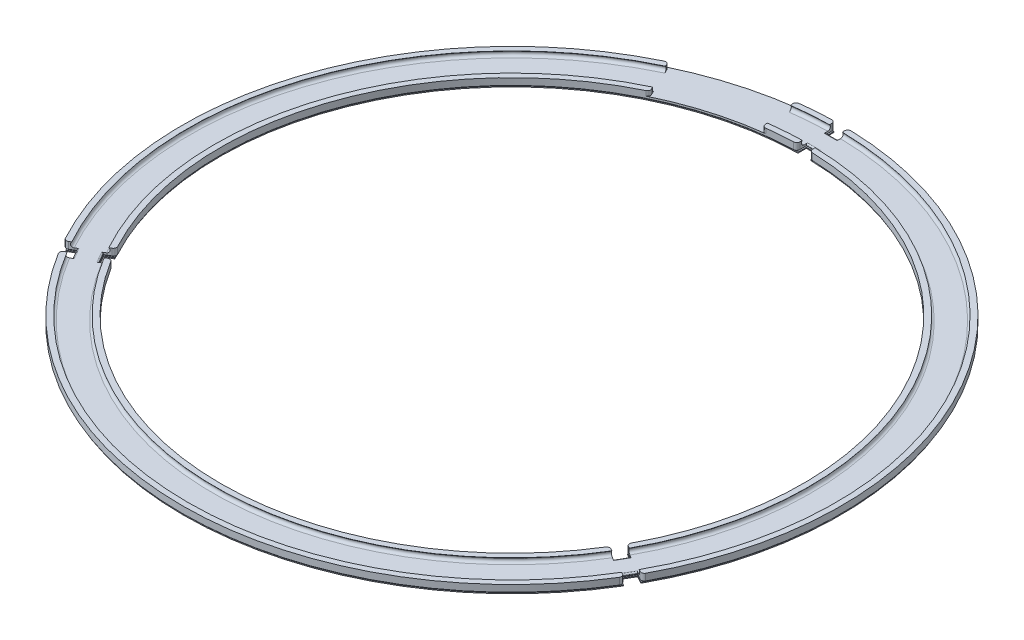
SolidWorks part; units mm, degrees
other "ferrite_sheet"
other "inductive_coil_frame" parameters "D1"=157.7465, "D2"=9.4909, "D3"=13.3244, "D4"=4.0567, "D5"=1.45, "D6"=1.6886
material "ABS"
ref_plane "Front Plane" through (0, 0, 0) normal (0, 0, 1) x (1, 0, 0)
ref_plane "Top Plane" through (0, 0, 0) normal (0, 1, 0) x (1, 0, 0)
ref_plane "Right Plane" through (0, 0, 0) normal (1, 0, 0) x (0, 0, -1)
sketch "Sketch1" plane through (0, 0, 0) normal (0, 0, 1) x (1, 0, 0)
  line L0 (0, 52.6316) -> (0, -56.2554) construction
  line L1 (93.5, 0) -> (100.9, 0) construction
  line L2 (91.2, 0.65) -> (92.9523, 0.65)
  line L3 (91.2, 0.65) -> (91.2, -1.85)
  line L4 (91.2, -1.85) -> (103.2, -1.85)
  line L5 (103.2, -1.85) -> (103.2, 0.65)
  line L6 (101.4477, 0.65) -> (103.2, 0.65)
  line L7 (93.5, -0.85) -> (100.9, -0.85)
  arc A0 (93.5, -0.85) -> (92.9523, 0.65) centre (93.5, 0) cw
  arc A1 (101.4477, 0.65) -> (100.9, -0.85) centre (100.9, 0) cw
  point P3 (92.65, 0)
  point P4 (92.9523, 0.65)
  point P14 (101.75, 0)
  point P16 (97.2, -1.85)
  point P17 (97.2, 0)
  dimension "D3" = 12
  dimension "D1" = 9.1
  dimension "D2" = 1.7
  dimension "D4" = 1
  dimension "D5" = 203.5
  dimension "D6" = 0.65
revolve "Revolve1" add sketch "Sketch1" angle 360 about L0
chamfer "Chamfer1" distance 0.4 angle 45 2 edges at (0, -1.85, 91.2) (0, -1.85, 103.2)
sketch "Sketch10" plane through (0, -1.85, 0) normal (0, -1, 0) x (1, 0, 0)
  circle A4 centre (0, 0) radius 91.6 construction
  circle A5 centre (0, 0) radius 102.8 construction
  circle A6 centre (0, 0) radius 91.6
  circle A7 centre (0, 0) radius 102.8
extrude "Boss-Extrude2" add sketch "Sketch10" along normal blind 0.3 separate body
sketch "Sketch11" plane through (0, 0, 0) normal (0, 1, 0) x (1, 0, 0)
  line L0 (-2, 103.1806) -> (-2, 100.1793)
  line L1 (-2, 100.1793) -> (2, 100.1793)
  line L2 (2, 100.1793) -> (2, 103.1806)
  line L3 (-2, 91.1781) -> (-2, 94.1793)
  line L4 (-2, 94.1793) -> (2, 94.1793)
  line L5 (2, 94.1793) -> (2, 91.1781)
  line L6 (-2, 100.1793) -> (-2, 94.1793) construction
  circle A0 centre (0, 0) radius 103.2 construction
  circle A1 centre (0, 0) radius 91.2 construction
  arc A2 (2, 91.1781) -> (-2, 91.1781) centre (0, 0) ccw
  arc A3 (2, 103.1806) -> (-2, 103.1806) centre (0, 0) ccw
  point P2 (0, 100.1793)
  dimension "D1" = 4
  dimension "D2" = 6
extrude "Cut-Extrude5" cut sketch "Sketch11" against normal through all both and the other way through all
fillet "Fillet4" radius 1 4 edges at (2, -0.4, -103.1806) (2, -0.4, -91.1781) (-2, -0.4, -103.1806) (-2, -0.4, -91.1781)
chamfer "Chamfer2" distance 0.4 angle 45 10 edges at (-2.0554, -1.85, -102.4842) (2.0554, -1.85, -102.4842) (-2, -1.85, -101.1677) (0, -1.85, -100.1793) (2, -1.85, -101.1677) (-2.047, -1.85, -91.8484) (2.047, -1.85, -91.8484) (-2, -1.85, -93.1653) (0, -1.85, -94.1793) (2, -1.85, -93.1653)
fillet "Fillet6" radius 0.4 2 edges at (0, -0.85, -94.1793) (0, -0.85, -100.1793)
pattern_circular "CirPattern3" count 3 over 360 about axis through (0, 0, 0) along (0, 1, 0) of "Fillet4", "Cut-Extrude5", "Chamfer2", "Fillet6"
sketch "Sketch12" plane through (0, -0.85, 0) normal (0, 1, 0) x (1, 0, 0)
  line L0 (-44.2644, 93.225) -> (0, 0)
  line L1 (0, 0) -> (-13.5789, 102.3027)
  line L3 (0, 0) -> (0, 129.8697) construction
  line L4 (-6, 87.0346) -> (-6, 73.3546) construction
  arc A0 (90.85, -48.9543) -> (3.0294, 103.1555) centre (0, 0) ccw construction
  arc A1 (-13.5789, 102.3027) -> (-44.2644, 93.225) centre (0, 0) ccw
  arc A3 (-2.9675, 91.1517) -> (-80.4234, -43.006) centre (0, 0) ccw construction
  point P1 (-12, 90.4071)
  point P2 (-12.0004, 90.407)
  dimension "D1" = 6
  dimension "D2" = 6
  dimension "D3" = 32
extrude "Cut-Extrude6" cut sketch "Sketch12" along normal through all
fillet "Fillet5" radius 1 4 edges at (-13.5789, -0.1, -102.3027) (-12, -0.1, -90.4071) (-39.1173, -0.1, -82.3849) (-44.2644, -0.1, -93.225)
equation "\"ferrite_width\"= 12mm"
equation "\"D3@Sketch1\"=\"ferrite_width\""
equation "\"diameter\"= 203.5mm"
equation "\"D5@Sketch1\"=\"diameter\""
